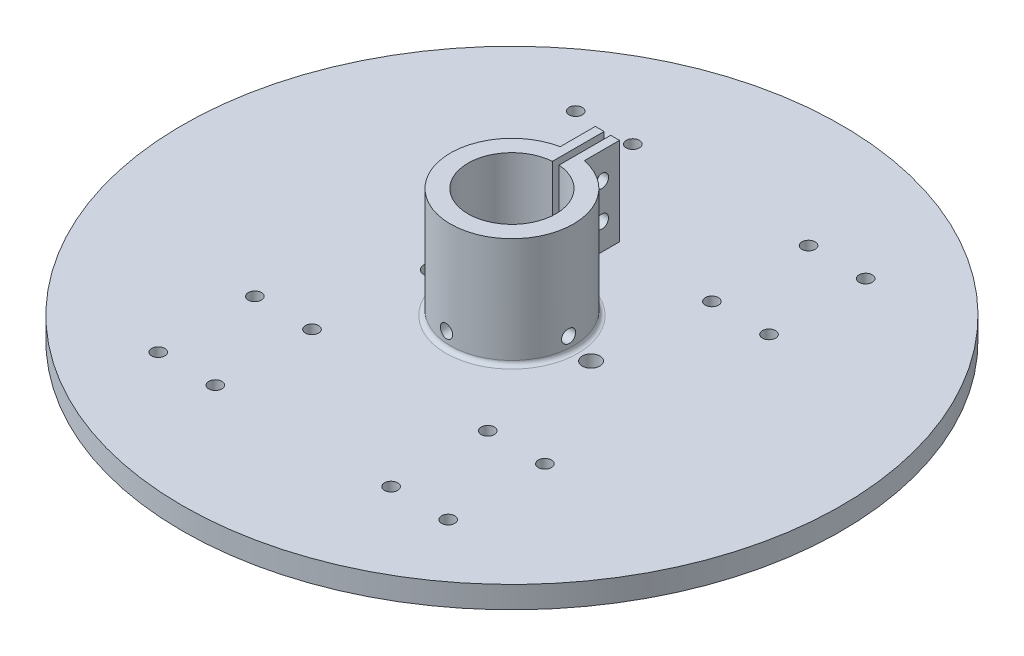
SolidWorks part; units mm, degrees
ref_plane "Front Plane" through (0, 0, 0) normal (0, 0, 1) x (1, 0, 0)
ref_plane "Top Plane" through (0, 0, 0) normal (0, 1, 0) x (1, 0, 0)
ref_plane "Right Plane" through (0, 0, 0) normal (1, 0, 0) x (0, 0, -1)
sketch "Sketch1" plane through (0, 0, 0) normal (0, 1, 0) x (1, 0, 0)
  circle A0 centre (0, 0) radius 75
  dimension "D1" = 150
extrude "Boss-Extrude1" add sketch "Sketch1" along normal blind 5
sketch "Sketch2" plane through (0, 5, 0) normal (0, 1, 0) x (1, 0, 0)
  circle A0 centre (0, 0) radius 14
  circle A1 centre (0, 0) radius 4
  circle A2 centre (0, 0) radius 10
  dimension "D1" = 8
  dimension "D2" = 28
  dimension "D3" = 20
extrude "Boss-Extrude2" add sketch "Sketch2" along normal blind 25 contours A0 A2 | A1
sketch "Sketch3" plane through (0, 30, 0) normal (0, 1, 0) x (1, 0, 0)
  circle A0 centre (0, 0) radius 4
  dimension "D1" = 8
extrude "Cut-Extrude1" cut sketch "Sketch3" against normal blind 12
ref_plane "Plane1" through (14, 0, 0) normal (1, 0, 0) x (0, 0, -1)
sketch "Sketch4" plane through (14, 0, 0) normal (1, 0, 0) x (0, 0, -1)
  line L1 (14, 5) -> (-14, 5) construction
  line L2 (14, 5) -> (14, 30) construction
  circle A0 centre (-1, 8.4) radius 1.5
  dimension "D1" = 3
  dimension "D2" = 3.4
  dimension "D3" = 15
extrude "Cut-Extrude2" cut sketch "Sketch4" against normal up to next
ref_plane "Plane2" through (0, 0, 14) normal (0, 0, 1) x (1, 0, 0)
sketch "Sketch5" plane through (0, 0, 14) normal (0, 0, 1) x (1, 0, 0)
  line L0 (14, -13.75) -> (14, 13.75) construction
  line L1 (14, 5) -> (-14, 5) construction
  circle A0 centre (-1, 8.4) radius 1.5
  dimension "D1" = 3
  dimension "D2" = 15
  dimension "D3" = 3.4
extrude "Cut-Extrude3" cut sketch "Sketch5" against normal up to next
sketch "Sketch6" plane through (0, 0, 0) normal (0, -1, 0) x (1, 0, 0)
  line L0 (-106.3466, 0) -> (112.8257, 0) construction
  line L1 (0, 87.2444) -> (0, -91.9362) construction
  circle A0 centre (-18, 0) radius 2
  circle A1 centre (18, 0) radius 2
  dimension "D1" = 18
  dimension "D2" = 18
  dimension "D3" = 4
extrude "Cut-Extrude4" cut sketch "Sketch6" against normal through all
sketch "Sketch7" plane through (0, 0, 0) normal (0, -1, 0) x (1, 0, 0)
  line L0 (0, 78.8593) -> (0, -84.0957) construction
  line L1 (-106.193, 0) -> (115.409, 0) construction
  line L2 (-83.4138, 36.5) -> (98.0235, 36.5) construction
  line L3 (26.5, 95.648) -> (26.5, -42.6819) construction
  circle A0 centre (20, 47.5) radius 1.5
  circle A2 centre (33, 47.5) radius 1.5
  circle A3 centre (20, 25.5) radius 1.5
  circle A4 centre (33, 25.5) radius 1.5
  circle A5 centre (-20, 25.5) radius 1.5
  circle A6 centre (-33, 25.5) radius 1.5
  circle A7 centre (-33, 47.5) radius 1.5
  circle A8 centre (-20, 47.5) radius 1.5
  circle A9 centre (-33, -47.5) radius 1.5
  circle A10 centre (-20, -47.5) radius 1.5
  circle A11 centre (-20, -25.5) radius 1.5
  circle A12 centre (-33, -25.5) radius 1.5
  circle A13 centre (20, -25.5) radius 1.5
  circle A14 centre (20, -47.5) radius 1.5
  circle A15 centre (33, -47.5) radius 1.5
  circle A16 centre (33, -25.5) radius 1.5
  dimension "D1" = 20
  dimension "D2" = 3
  dimension "D3" = 47.5
  dimension "D4" = 36.5
  dimension "D5" = 26.5
extrude "Cut-Extrude5" cut sketch "Sketch7" against normal through all
sketch "Sketch8" plane through (0, 30, 0) normal (0, 1, 0) x (1, 0, 0)
  line L0 (0, 61.0557) -> (0, -64.1976) construction
  line L1 (-56.5525, 0) -> (50.8972, 0) construction
  line L2 (0.75, 13.9799) -> (0.75, 9.9718)
  line L3 (-0.75, 13.9799) -> (-0.75, 9.9718)
  circle A2 centre (0, 0) radius 14 construction
  circle A3 centre (0, 0) radius 10 construction
  arc A4 (0.75, 13.9799) -> (-0.75, 13.9799) centre (0, 0) ccw
  arc A5 (0.75, 9.9718) -> (-0.75, 9.9718) centre (0, 0) ccw
  dimension "D2" = 14
  dimension "D3" = 10
  dimension "D1" = 0.75
extrude "Cut-Extrude6" cut sketch "Sketch8" against normal up to surface (25 mm away) up to face at (-33, 5, 27)
sketch "Sketch9" plane through (0, 30, 0) normal (0, 1, 0) x (1, 0, 0)
  line L0 (0, 20.0372) -> (0, -1.2241) construction
  line L1 (0.75, 13.9799) -> (0.75, 21.7273)
  line L2 (0.75, 21.7273) -> (2.75, 21.7273)
  line L3 (2.75, 21.7273) -> (2.75, 13.7273)
  line L4 (-0.75, 21.7273) -> (-2.75, 21.7273)
  line L5 (-2.75, 21.7273) -> (-2.75, 13.7273)
  line L6 (-0.75, 13.9799) -> (-0.75, 21.7273)
  arc A0 (-0.75, 13.9799) -> (0.75, 13.9799) centre (0, 0) ccw construction
  arc A1 (2.75, 13.7273) -> (0.75, 13.9799) centre (0, 0) ccw
  arc A2 (-2.75, 13.7273) -> (-0.75, 13.9799) centre (0, 0) cw
  dimension "D1" = 2
  dimension "D2" = 8
extrude "Boss-Extrude3" add sketch "Sketch9" against normal blind 20
sketch "Sketch10" plane through (2.75, 0, 0) normal (1, 0, 0) x (0, 0, -1)
  line L0 (13.7273, 10) -> (21.7273, 10) construction
  line L1 (13.7273, 30) -> (21.7273, 30) construction
  line L2 (13.7273, 10) -> (13.7273, 30) construction
  circle A0 centre (17.7273, 24) radius 1.5
  circle A1 centre (17.7273, 16) radius 1.5
  dimension "D1" = 3
  dimension "D2" = 6
  dimension "D3" = 6
  dimension "D4" = 4
extrude "Cut-Extrude7" cut sketch "Sketch10" against normal through all
fillet "Fillet1" radius 1 1 edges at (0, 5, 14)
